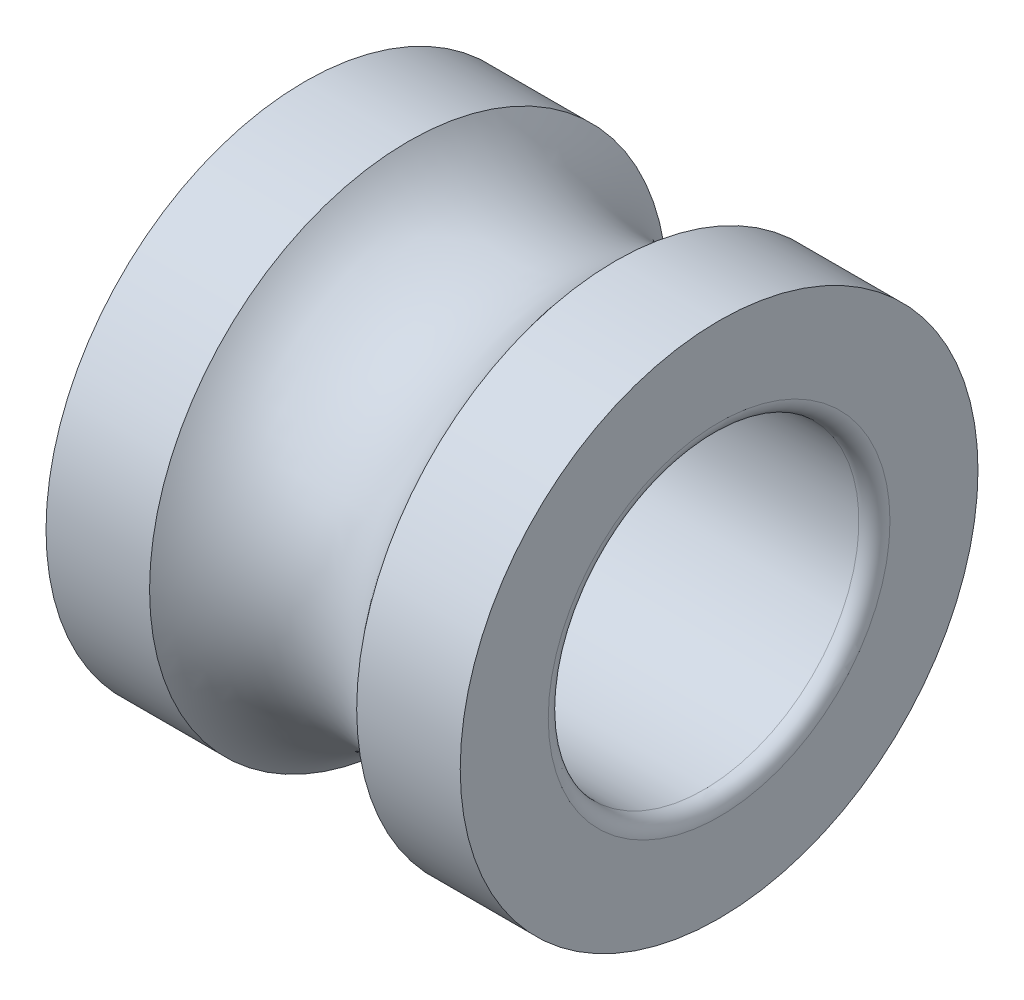
SolidWorks part; units mm, degrees
ref_plane "Plan1" through (0, 0, 0) normal (0, 0, 1) x (1, 0, 0)
ref_plane "Plan2" through (0, 0, 0) normal (0, 1, 0) x (1, 0, 0)
ref_plane "Plan3" through (0, 0, 0) normal (1, 0, 0) x (0, 0, -1)
sketch "Esquisse1" plane through (0, 0, 0) normal (0, 0, 1) x (1, 0, 0)
  line L0 (0, 1.5) -> (0, 2.5) construction
  line L1 (0, 2.5) -> (1, 2.5) construction
  line L2 (3, 2.5) -> (4, 2.5) construction
  line L3 (4, 1.5) -> (4, 2.5) construction
  line L4 (0, 1.5) -> (4, 1.5) construction
  line L5 (0, 1.5) -> (0, 2.5)
  line L6 (0, 2.5) -> (1, 2.5)
  line L7 (3, 2.5) -> (4, 2.5)
  line L8 (4, 1.5) -> (4, 2.5)
  line L9 (0, 1.5) -> (4, 1.5)
  line L10 (0, 0) -> (6.0033, 0) construction
  line L11 (0, 0) -> (7.3387, 0) construction
  circle A0 centre (2, 3.25) radius 1.25 construction
  arc A1 (1, 2.5) -> (3, 2.5) centre (2, 3.25) ccw
revolve "Base-Révolution" add sketch "Esquisse1" angle 360 about L10
fillet "Congé1" radius 0.15
